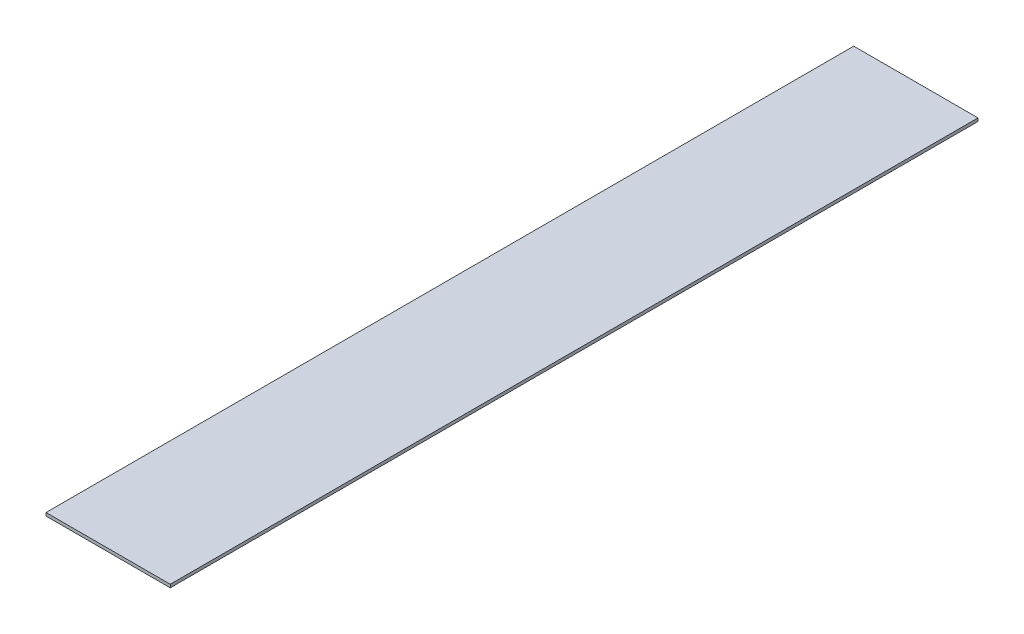
SolidWorks part; units mm, degrees
ref_plane "Front Plane" through (0, 0, 0) normal (0, 0, 1) x (1, 0, 0)
ref_plane "Top Plane" through (0, 0, 0) normal (0, 1, 0) x (1, 0, 0)
ref_plane "Right Plane" through (0, 0, 0) normal (1, 0, 0) x (0, 0, -1)
sketch "Sketch1" plane through (0, 0, 0) normal (0, 1, 0) x (1, 0, 0)
  line L1 (-25.4, -165.1) -> (25.4, -165.1)
  line L2 (-25.4, -165.1) -> (-25.4, 165.1)
  line L3 (-25.4, 165.1) -> (25.4, 165.1)
  line L4 (25.4, -165.1) -> (25.4, 165.1)
  line L5 (-25.4, -165.1) -> (25.4, 165.1) construction
  line L6 (-25.4, 165.1) -> (25.4, -165.1) construction
  point P0 (0, 0)
  dimension "D1" = 50.8
  dimension "D2" = 330.2
extrude "Boss-Extrude1" add sketch "Sketch1" along normal blind 1.27 contours L2 L3 L4 L1
